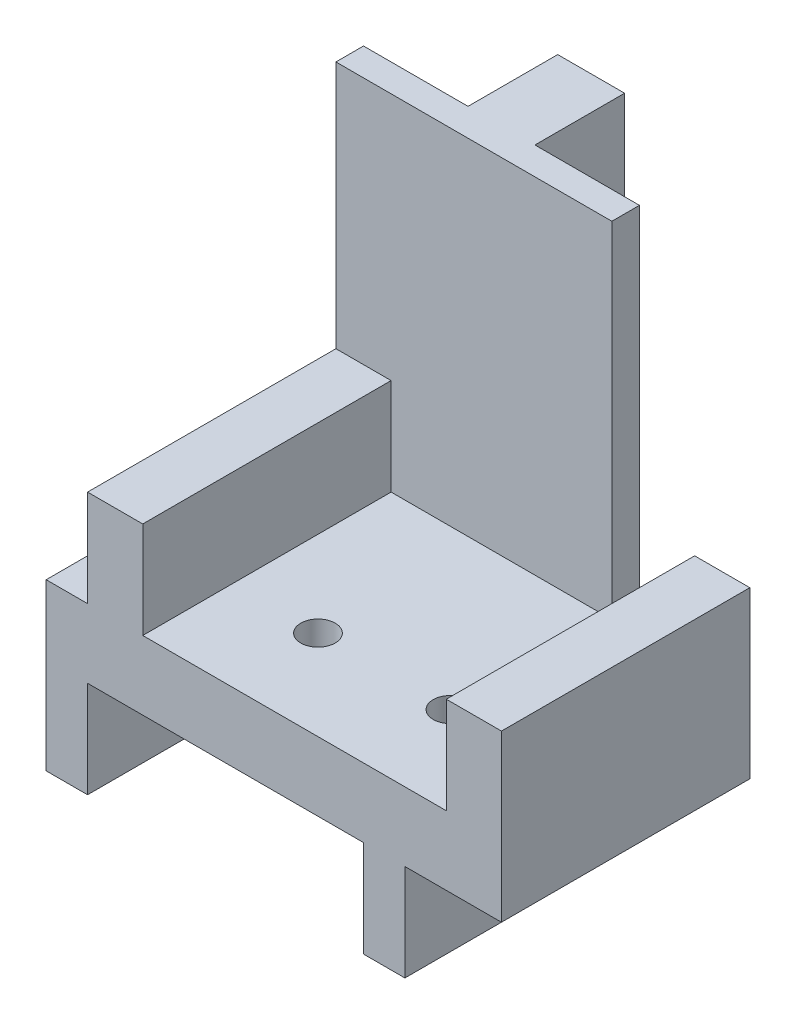
SolidWorks part; units mm, degrees
ref_plane "정면" through (0, 0, 0) normal (0, 0, 1) x (1, 0, 0)
ref_plane "윗면" through (0, 0, 0) normal (0, 1, 0) x (1, 0, 0)
ref_plane "우측면" through (0, 0, 0) normal (1, 0, 0) x (0, 0, -1)
sketch "스케치1" plane through (0, 0, 0) normal (0, 0, 1) x (1, 0, 0)
  line L0 (-15, 12) -> (-15, 0)
  line L1 (-15, 0) -> (15, 0)
  line L2 (15, 0) -> (15, 12)
  line L3 (15, 12) -> (11, 12)
  line L4 (11, 12) -> (11, 5)
  line L5 (11, 5) -> (-11, 5)
  line L6 (-11, 5) -> (-11, 12)
  line L7 (-11, 12) -> (-15, 12)
  point P7 (0, 0)
  dimension "D1" = 30
  dimension "D2" = 4
  dimension "D3" = 5
  dimension "D4" = 12
extrude "보스-돌출1" add sketch "스케치1" along normal blind 18 contours L5 L6 L7 L0 L1 L2 L3 L4
sketch "스케치3" plane through (0, 0, 0) normal (0, 0, -1) x (-1, 0, 0)
  line L1 (15, 0) -> (-5, 0)
  line L2 (15, 0) -> (15, 30)
  line L3 (15, 30) -> (-5, 30)
  line L4 (-5, 0) -> (-5, 30)
  line L5 (15, 0) -> (-5, 30) construction
  line L6 (15, 30) -> (-5, 0) construction
  point P4 (5, 15)
  dimension "D1" = 20
  dimension "D2" = 30
extrude "보스-돌출2" add sketch "스케치3" along normal blind 2
sketch "스케치4" plane through (0, 0, -2) normal (0, 0, -1) x (-1, 0, 0)
  line L0 (15, 30) -> (-5, 30) construction
  line L1 (2.575, 30) -> (7.425, 30)
  line L2 (2.575, 30) -> (2.575, 0)
  line L3 (2.575, 0) -> (7.425, 0)
  line L4 (7.425, 30) -> (7.425, 0)
  line L5 (2.575, 30) -> (7.425, 0) construction
  line L6 (2.575, 0) -> (7.425, 30) construction
  line L7 (-5, 0) -> (15, 0) construction
  line L8 (5, 30) -> (5, 0) construction
  point P4 (5, 15)
  dimension "D1" = 4.85
extrude "보스-돌출3" add sketch "스케치4" along normal blind 6.5
sketch "스케치5" plane through (0, 0, 18) normal (0, 0, 1) x (1, 0, 0)
  line L0 (-15, 12) -> (-15, 0) construction
  line L1 (-15, 5) -> (-18, 5)
  line L2 (-15, 5) -> (-15, -7)
  line L3 (-15, -7) -> (-18, -7)
  line L4 (-18, 5) -> (-18, -7)
  line L5 (-15, 5) -> (-18, -7) construction
  line L6 (-15, -7) -> (-18, 5) construction
  line L7 (5, 5) -> (-11, 5) construction
  line L8 (5, 5) -> (8, 5)
  line L9 (5, 5) -> (5, -7)
  line L10 (5, -7) -> (8, -7)
  line L11 (8, 5) -> (8, -7)
  line L12 (5, 5) -> (8, -7) construction
  line L13 (5, -7) -> (8, 5) construction
  point P4 (-16.5, -1)
  point P11 (6.5, -1)
  dimension "D1" = 3
  dimension "D2" = 12
extrude "보스-돌출4" add sketch "스케치5" against normal up to vertex
sketch "스케치2" plane through (0, 5, 0) normal (0, 1, 0) x (1, 0, 0)
  line L0 (0, 0) -> (0, -18) construction
  line L1 (11, -18) -> (-11, -18) construction
  circle A0 centre (-4.8, -11.5) radius 1.25
  circle A1 centre (4.8, -11.5) radius 1.25
  dimension "D1" = 2.5
  dimension "D2" = 6.5
  dimension "D3" = 4.8
extrude "컷-돌출1" cut sketch "스케치2" against normal blind 18
